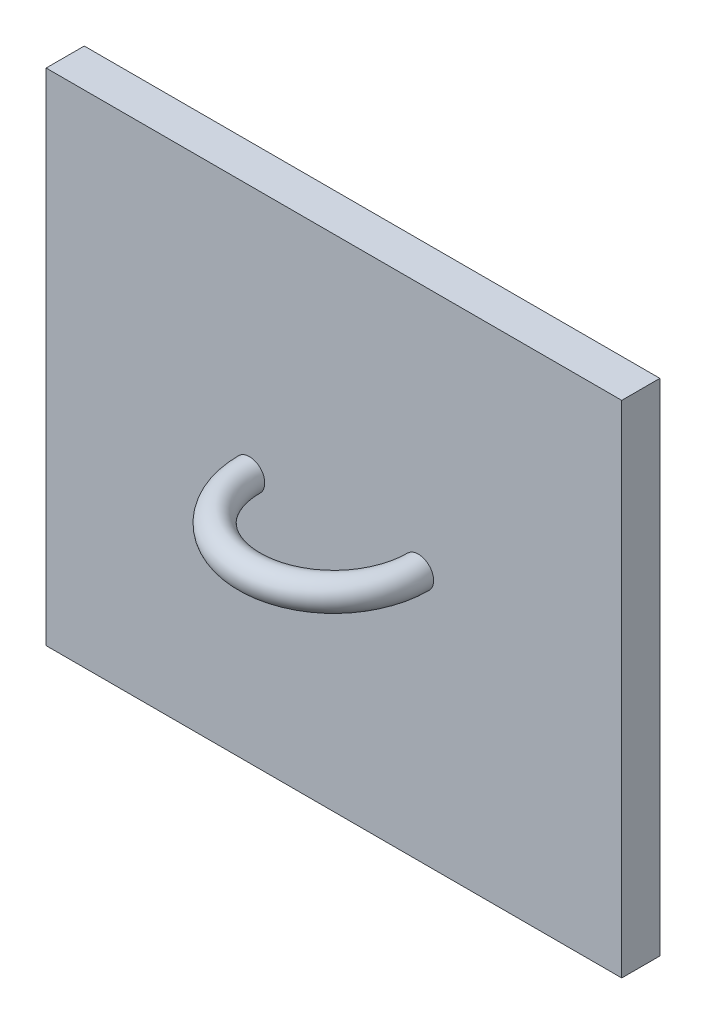
SolidWorks part; units mm, degrees
ref_plane "Front Plane" through (0, 0, 0) normal (0, 0, 1) x (1, 0, 0)
ref_plane "Top Plane" through (0, 0, 0) normal (0, 1, 0) x (1, 0, 0)
ref_plane "Right Plane" through (0, 0, 0) normal (1, 0, 0) x (0, 0, -1)
sketch "Sketch1" plane through (0, 0, 0) normal (0, 0, 1) x (1, 0, 0)
  line L1 (0, 0) -> (188.7, 0)
  line L2 (0, 0) -> (0, 164)
  line L3 (0, 164) -> (188.7, 164)
  line L4 (188.7, 0) -> (188.7, 164)
  dimension "D1" = 188.7
  dimension "D2" = 164
extrude "Boss-Extrude1" add sketch "Sketch1" along normal blind 12.5
sketch "Sketch2" plane through (0, 0, 12.5) normal (0, 0, 1) x (1, 0, 0)
  line L0 (94.35, 164) -> (94.35, 0) construction
  line L1 (188.7, 164) -> (0, 164) construction
  line L2 (0, 0) -> (188.7, 0) construction
sketch "Sketch3" plane through (0, 0, 12.5) normal (0, 0, 1) x (1, 0, 0)
  line L0 (0, 0) -> (188.7, 0) construction
  circle A0 centre (66.6762, 82) radius 5
  dimension "D1" = 10
  dimension "D2" = 82
revolve "Revolve1" add sketch "Sketch3" angle 180 about L0
